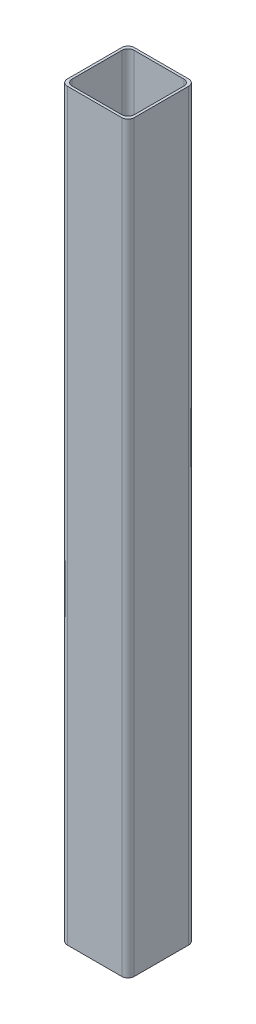
SolidWorks part; units mm, degrees
material "Carbon Fiber"
ref_plane "Front Plane" through (0, 0, 0) normal (0, 0, 1) x (1, 0, 0)
ref_plane "Top Plane" through (0, 0, 0) normal (0, 1, 0) x (1, 0, 0)
ref_plane "Right Plane" through (0, 0, 0) normal (1, 0, 0) x (0, 0, -1)
sketch "Sketch1" plane through (0, 0, 0) normal (0, 1, 0) x (1, 0, 0)
  line L1 (-10.16, -12.7) -> (10.16, -12.7)
  line L2 (-12.7, -10.16) -> (-12.7, 10.16)
  line L3 (-10.16, 12.7) -> (10.16, 12.7)
  line L4 (12.7, -10.16) -> (12.7, 10.16)
  line L5 (-12.7, -12.7) -> (12.7, 12.7) construction
  line L6 (-12.7, 12.7) -> (12.7, -12.7) construction
  line L7 (-11.176, -13.716) -> (11.176, -13.716)
  line L8 (-13.716, -11.176) -> (-13.716, 11.176)
  line L9 (-11.176, 13.716) -> (11.176, 13.716)
  line L10 (13.716, -11.176) -> (13.716, 11.176)
  line L11 (-13.716, -13.716) -> (13.716, 13.716) construction
  line L12 (-13.716, 13.716) -> (13.716, -13.716) construction
  arc A0 (13.716, 11.176) -> (11.176, 13.716) centre (11.176, 11.176) ccw
  arc A1 (13.716, -11.176) -> (11.176, -13.716) centre (11.176, -11.176) cw
  arc A2 (-11.176, -13.716) -> (-13.716, -11.176) centre (-11.176, -11.176) cw
  arc A3 (-13.716, 11.176) -> (-11.176, 13.716) centre (-11.176, 11.176) cw
  arc A4 (12.7, -10.16) -> (10.16, -12.7) centre (10.16, -10.16) cw
  arc A5 (-10.16, -12.7) -> (-12.7, -10.16) centre (-10.16, -10.16) cw
  arc A6 (12.7, 10.16) -> (10.16, 12.7) centre (10.16, 10.16) ccw
  arc A7 (-10.16, 12.7) -> (-12.7, 10.16) centre (-10.16, 10.16) ccw
  point P0 (0, 0)
  point P6 (0, 0)
  dimension "D5" = 2.54
  dimension "D1" = 25.4
  dimension "D2" = 25.4
  dimension "D3" = 27.432
  dimension "D4" = 27.432
extrude "Boss-Extrude1" add sketch "Sketch1" along normal blind 304.8
